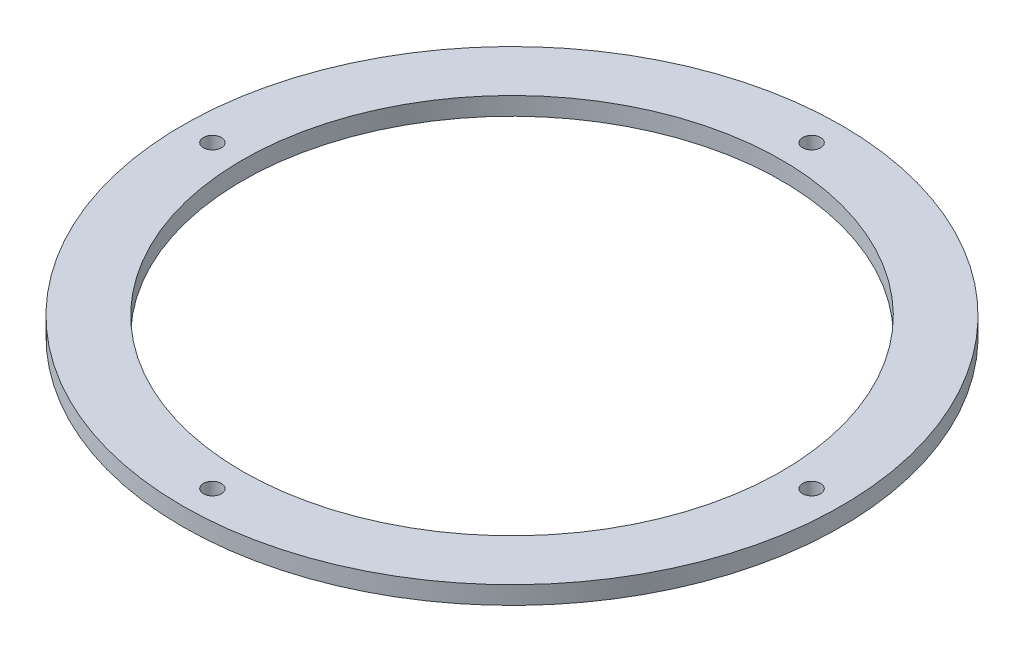
SolidWorks part; units mm, degrees
ref_plane "Front Plane" through (0, 0, 0) normal (0, 0, 1) x (1, 0, 0)
ref_plane "Top Plane" through (0, 0, 0) normal (0, 1, 0) x (1, 0, 0)
ref_plane "Right Plane" through (0, 0, 0) normal (1, 0, 0) x (0, 0, -1)
sketch "Sketch1" plane through (0, 0, 0) normal (0, 1, 0) x (1, 0, 0)
  circle A0 centre (0, 0) radius 55
  circle A1 centre (0, 0) radius 45
  dimension "D1" = 90
  dimension "D2" = 110
extrude "Boss-Extrude1" add sketch "Sketch1" along normal blind 3
sketch "Sketch2" plane through (0, 3, 0) normal (0, 1, 0) x (1, 0, 0)
  line L0 (0, 55) -> (0, 45) construction
  line L1 (45, 0) -> (55, 0) construction
  line L2 (0, -45) -> (0, -55) construction
  line L3 (-55, 0) -> (-45, 0) construction
  circle A0 centre (0, 0) radius 55 construction
  circle A1 centre (0, 0) radius 45 construction
  circle A2 centre (-50, 0) radius 1.5
  circle A3 centre (0, -50) radius 1.5
  circle A4 centre (50, 0) radius 1.5
  circle A5 centre (0, 50) radius 1.5
  dimension "D1" = 3
  dimension "D2" = 3
  dimension "D3" = 3
  dimension "D4" = 3
extrude "Cut-Extrude1" cut sketch "Sketch2" against normal blind 3
